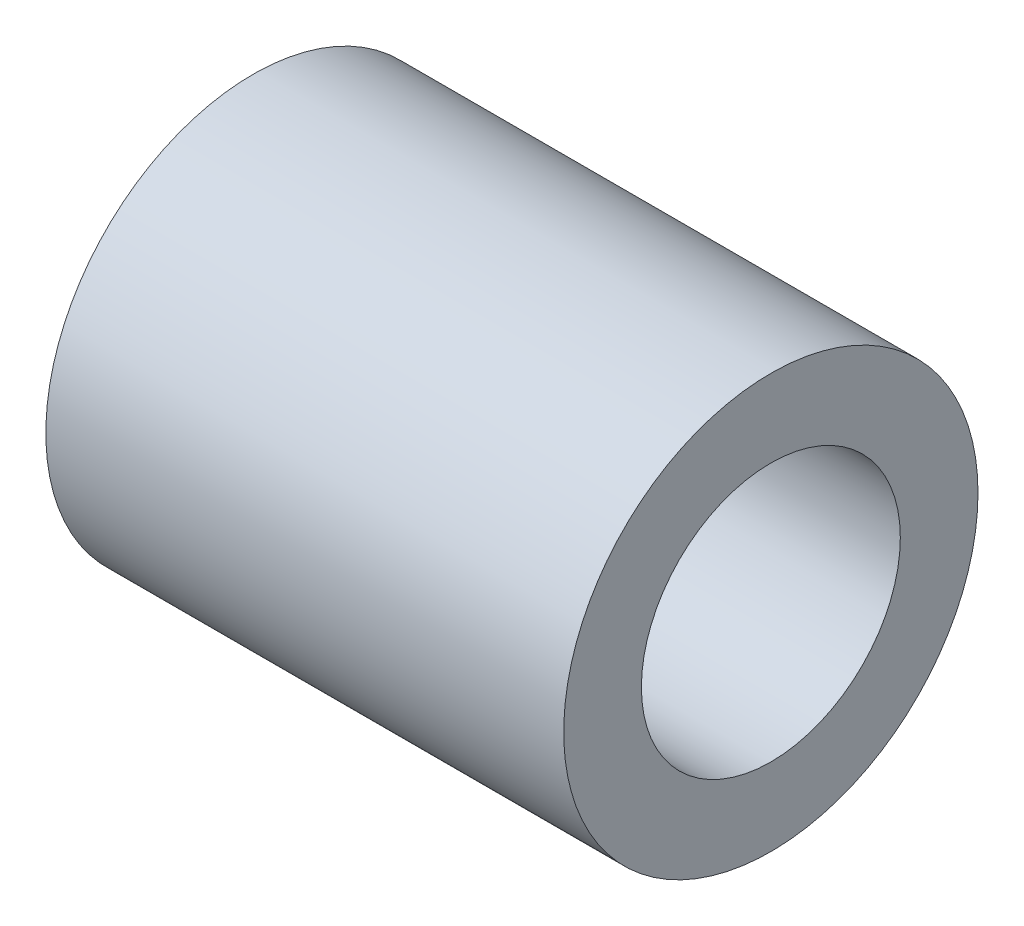
SolidWorks part; units mm, degrees
ref_plane "前视基准面" through (0, 0, 0) normal (0, 0, 1) x (1, 0, 0)
ref_plane "上视基准面" through (0, 0, 0) normal (0, 1, 0) x (1, 0, 0)
ref_plane "右视基准面" through (0, 0, 0) normal (1, 0, 0) x (0, 0, -1)
sketch "草图1" plane through (0, 0, 0) normal (1, 0, 0) x (0, 0, -1)
  circle A0 centre (0, 0) radius 4
  circle A1 centre (0, 0) radius 2.5
extrude "凸台-拉伸1" add sketch "草图1" along normal blind 10
